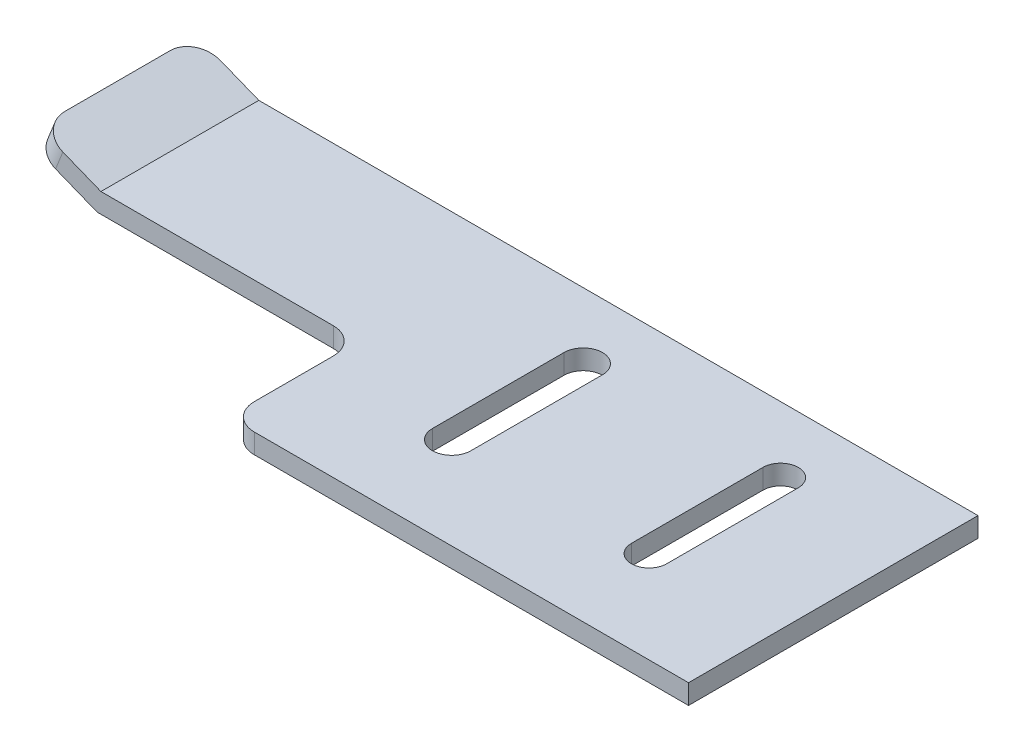
SolidWorks part; units mm, degrees
ref_plane "Front Plane" through (0, 0, 0) normal (0, 0, 1) x (1, 0, 0)
ref_plane "Top Plane" through (0, 0, 0) normal (0, 1, 0) x (1, 0, 0)
ref_plane "Right Plane" through (0, 0, 0) normal (1, 0, 0) x (0, 0, -1)
sketch "Sketch1" plane through (0, 0, 0) normal (0, 0, 1) x (1, 0, 0)
  line L0 (-2.5319, 4.3781) -> (-7.5462, 6.3822)
  line L1 (-2.2433, 5.8781) -> (52.4138, 5.8781)
  line L2 (-7.5462, 6.3822) -> (-6.9895, 7.7751)
  line L3 (-2.5319, 4.3781) -> (52.4138, 4.3781)
  line L4 (52.4138, 5.8781) -> (52.4138, 4.3781)
  line L5 (-6.9895, 7.7751) -> (-2.2433, 5.8781)
  dimension "D1" = 1.5
  dimension "D2" = 1.5
  dimension "D3" = 5.4
  dimension "D4" = 59.96
extrude "Boss-Extrude1" add sketch "Sketch1" along normal blind 22
sketch "Sketch2" plane through (0, 4.3781, 0) normal (0, -1, 0) x (1, 0, 0)
  line L0 (-2.5319, 0) -> (52.4138, 0) construction
  line L1 (-2.5319, 22) -> (52.4138, 22) construction
  line L2 (17.4138, 22) -> (-14.9109, 22)
  line L3 (17.4138, 22) -> (17.4138, 12)
  line L4 (17.4138, 12) -> (-14.9109, 12)
  line L5 (52.4138, 22) -> (52.4138, 0) construction
  line L6 (27.4138, 15) -> (27.4138, 5) construction
  line L7 (28.8769, 15) -> (28.8769, 5)
  line L8 (25.9506, 15) -> (25.9506, 5)
  line L9 (42.4138, 15) -> (42.4138, 5) construction
  line L10 (43.7571, 15) -> (43.7571, 5)
  line L11 (41.0705, 15) -> (41.0705, 5)
  line L12 (-14.9109, 22) -> (-14.9109, 12)
  arc A0 (28.8769, 15) -> (25.9506, 15) centre (27.4138, 15) ccw
  arc A1 (25.9506, 5) -> (28.8769, 5) centre (27.4138, 5) ccw
  arc A2 (43.7571, 15) -> (41.0705, 15) centre (42.4138, 15) ccw
  arc A3 (41.0705, 5) -> (43.7571, 5) centre (42.4138, 5) ccw
  point P10 (27.4138, 10)
  point P15 (42.4138, 10)
  dimension "D1" = 35
  dimension "D2" = 10
  dimension "D3" = 5
  dimension "D4" = 10
  dimension "D5" = 5
  dimension "D6" = 10
  dimension "D7" = 10
  dimension "D8" = 25
extrude "Cut-Extrude1" cut sketch "Sketch2" against normal blind 22
fillet "Fillet2" radius 2 4 edges at (-7.2679, 7.0787, 0) (-7.2679, 7.0787, 12) (17.4138, 5.1281, 12) (17.4138, 5.1281, 22)
